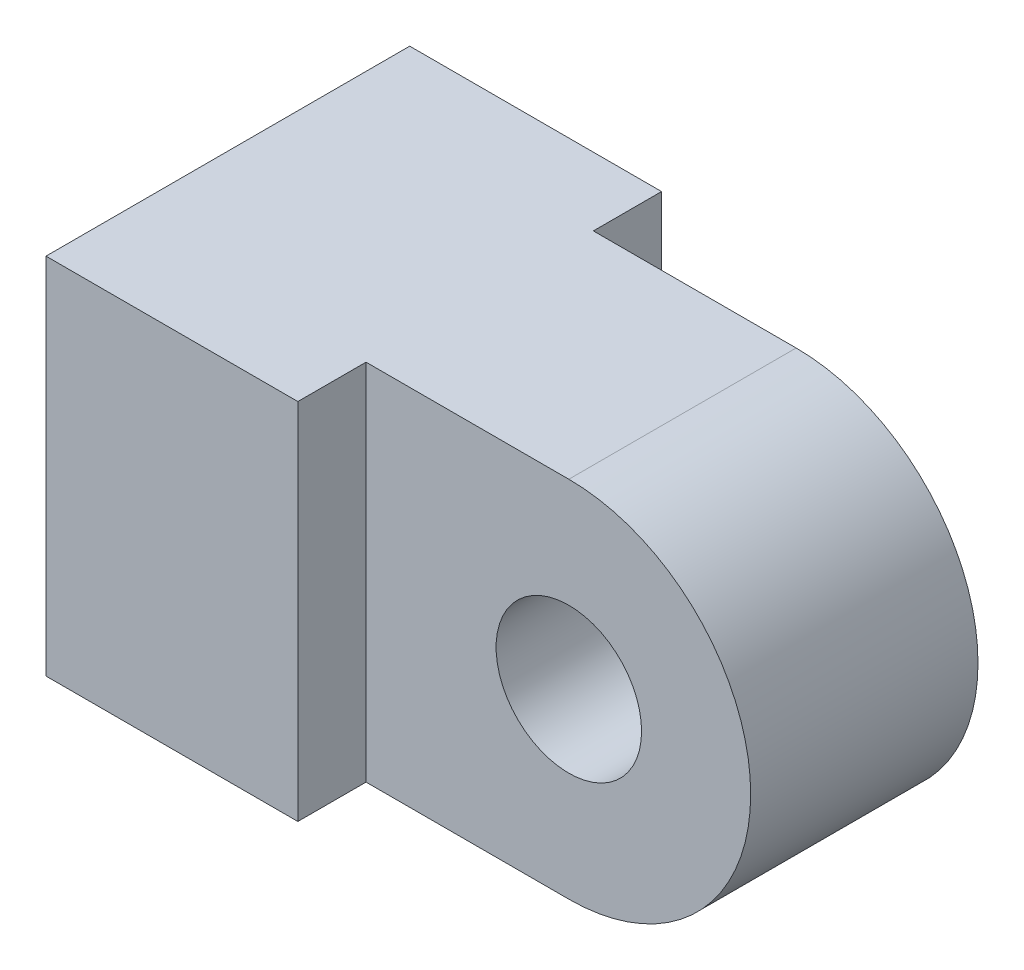
SolidWorks part; units mm, degrees
ref_plane "Front Plane" through (0, 0, 0) normal (0, 0, 1) x (1, 0, 0)
ref_plane "Top Plane" through (0, 0, 0) normal (0, 1, 0) x (1, 0, 0)
ref_plane "Right Plane" through (0, 0, 0) normal (1, 0, 0) x (0, 0, -1)
sketch "Sketch1" plane through (0, 0, 0) normal (0, 0, 1) x (1, 0, 0)
  line L0 (0, 4) -> (-10, 4)
  line L1 (-10, 4) -> (-10, -4)
  line L2 (0, -4) -> (-10, -4)
  circle A0 centre (0, 0) radius 1.6
  arc A1 (0, -4) -> (0, 4) centre (0, 0) ccw
  dimension "D1" = 8
  dimension "D2" = 3.2
  dimension "D3" = 10
extrude "Boss-Extrude2" add sketch "Sketch1" along normal blind 5
sketch "Sketch2" plane through (0, 0, 5) normal (0, 0, 1) x (1, 0, 0)
  line L0 (-4.4605, 4) -> (-4.4605, -4)
  line L1 (0, 4) -> (-10, 4) construction
  line L2 (-10, -4) -> (0, -4) construction
  line L3 (-4.4605, 4) -> (-10, 4)
  line L4 (-10, 4) -> (-10, -4)
  line L5 (-10, 4) -> (-10, -4) construction
  line L6 (-10, -4) -> (-4.4605, -4)
  circle A0 centre (0, 0) radius 4 construction
extrude "Boss-Extrude3" add sketch "Sketch2" along normal blind 1.5
sketch "Sketch3" plane through (0, 0, 0) normal (0, 0, -1) x (-1, 0, 0)
  line L0 (4.4605, 4) -> (4.4605, -4)
  line L1 (4.4605, -4) -> (10, -4)
  line L2 (10, -4) -> (10, 4)
  line L3 (10, 4) -> (4.4605, 4)
extrude "Boss-Extrude4" add sketch "Sketch3" along normal blind 1.5
